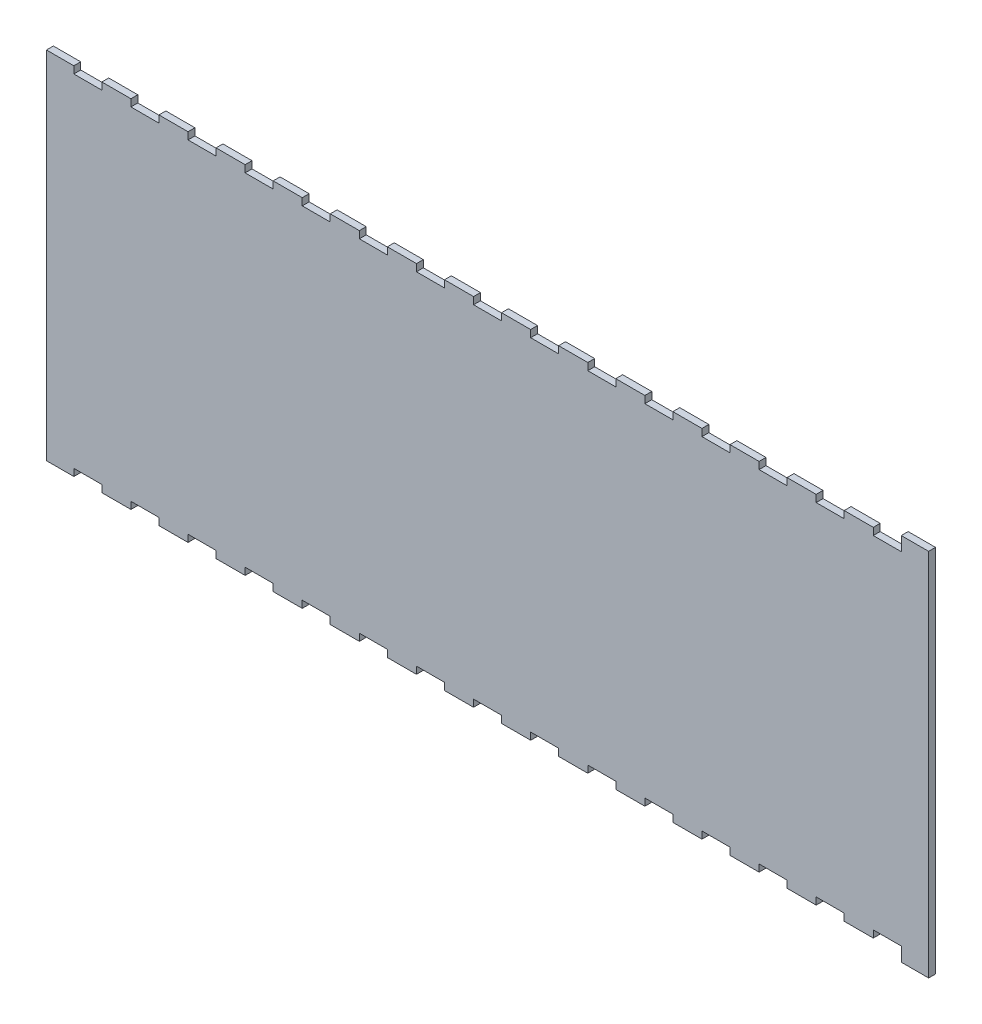
SolidWorks part; units mm, degrees
ref_plane "Front Plane" through (0, 0, 0) normal (0, 0, 1) x (1, 0, 0)
ref_plane "Top Plane" through (0, 0, 0) normal (0, 1, 0) x (1, 0, 0)
ref_plane "Right Plane" through (0, 0, 0) normal (1, 0, 0) x (0, 0, -1)
sketch "Sketch1" plane through (0, 0, 0) normal (0, 0, 1) x (1, 0, 0)
  line L248 (-12.6, 160.6058) -> (-25.5, 160.6058)
  line L249 (-25.5, 160.6058) -> (-25.5, 163.8808)
  line L250 (-25.5, 163.8808) -> (-38.9071, 163.8808)
  line L251 (-38.9071, 163.8808) -> (-38.9071, 160.6058)
  line L252 (-38.9071, 160.6058) -> (-51.8071, 160.6058)
  line L253 (-51.8071, 160.6058) -> (-51.8071, 163.8808)
  line L254 (-51.8071, 163.8808) -> (-65.2143, 163.8808)
  line L255 (-65.2143, 163.8808) -> (-65.2143, 160.6058)
  line L256 (-65.2143, 160.6058) -> (-78.1143, 160.6058)
  line L257 (-78.1143, 160.6058) -> (-78.1143, 163.8808)
  line L258 (-78.1143, 163.8808) -> (-91.5214, 163.8808)
  line L259 (-91.5214, 163.8808) -> (-91.5214, 160.6058)
  line L260 (-91.5214, 160.6058) -> (-104.4214, 160.6058)
  line L261 (-104.4214, 160.6058) -> (-104.4214, 163.8808)
  line L262 (-104.4214, 163.8808) -> (-117.8286, 163.8808)
  line L263 (-117.8286, 163.8808) -> (-117.8286, 160.6058)
  line L264 (-117.8286, 160.6058) -> (-130.7286, 160.6058)
  line L265 (-130.7286, 160.6058) -> (-130.7286, 163.8808)
  line L266 (-130.7286, 163.8808) -> (-144.1357, 163.8808)
  line L267 (-144.1357, 163.8808) -> (-144.1357, 160.6058)
  line L268 (-144.1357, 160.6058) -> (-157.0357, 160.6058)
  line L269 (-157.0357, 160.6058) -> (-157.0357, 163.8808)
  line L270 (-157.0357, 163.8808) -> (-170.4429, 163.8808)
  line L271 (-170.4429, 163.8808) -> (-170.4429, 160.6058)
  line L272 (-170.4429, 160.6058) -> (-183.3429, 160.6058)
  line L273 (-183.3429, 160.6058) -> (-183.3429, 163.8808)
  line L274 (-183.3429, 163.8808) -> (-196.75, 163.8808)
  line L275 (-196.75, 163.8808) -> (-196.75, 160.6058)
  line L276 (-196.75, 160.6058) -> (-209.65, 160.6058)
  line L277 (-209.65, 160.6058) -> (-209.65, 163.8808)
  line L278 (-209.65, 163.8808) -> (-223.0571, 163.8808)
  line L279 (-223.0571, 163.8808) -> (-223.0571, 160.6058)
  line L280 (-223.0571, 160.6058) -> (-235.9571, 160.6058)
  line L281 (-235.9571, 160.6058) -> (-235.9571, 163.8808)
  line L282 (-235.9571, 163.8808) -> (-249.3643, 163.8808)
  line L283 (-249.3643, 163.8808) -> (-249.3643, 160.6058)
  line L284 (-249.3643, 160.6058) -> (-262.2643, 160.6058)
  line L285 (-262.2643, 160.6058) -> (-262.2643, 163.8808)
  line L286 (-262.2643, 163.8808) -> (-275.6714, 163.8808)
  line L287 (-275.6714, 163.8808) -> (-275.6714, 160.6058)
  line L288 (-275.6714, 160.6058) -> (-288.5714, 160.6058)
  line L289 (-288.5714, 160.6058) -> (-288.5714, 163.8808)
  line L290 (-288.5714, 163.8808) -> (-301.9786, 163.8808)
  line L291 (-301.9786, 163.8808) -> (-301.9786, 160.6058)
  line L292 (-301.9786, 160.6058) -> (-314.8786, 160.6058)
  line L293 (-314.8786, 160.6058) -> (-314.8786, 163.8808)
  line L294 (-314.8786, 163.8808) -> (-328.2857, 163.8808)
  line L295 (-328.2857, 163.8808) -> (-328.2857, 160.6058)
  line L296 (-328.2857, 160.6058) -> (-341.1857, 160.6058)
  line L297 (-341.1857, 160.6058) -> (-341.1857, 163.8808)
  line L298 (-341.1857, 163.8808) -> (-354.5929, 163.8808)
  line L299 (-354.5929, 163.8808) -> (-354.5929, 160.6058)
  line L300 (-354.5929, 160.6058) -> (-367.4929, 160.6058)
  line L301 (-367.4929, 160.6058) -> (-367.4929, 163.8808)
  line L302 (-367.4929, 163.8808) -> (-380.9, 163.8808)
  line L303 (-380.9, 163.8808) -> (-380.9, 160.6058)
  line L304 (-380.9, 160.6058) -> (-393.8, 160.6058)
  line L305 (-393.8, 160.6058) -> (-393.8, 163.8808)
  line L306 (-393.8, 163.8808) -> (-406.4, 163.8808)
  line L307 (-406.4, 163.8808) -> (-406.4, 0)
  line L308 (-406.4, 0) -> (-393.8, 0)
  line L309 (-393.8, 0) -> (-393.8, 3.275)
  line L310 (-393.8, 3.275) -> (-380.9, 3.275)
  line L311 (-380.9, 3.275) -> (-380.9, 0)
  line L312 (-380.9, 0) -> (-367.4929, 0)
  line L313 (-367.4929, 0) -> (-367.4929, 3.275)
  line L314 (-367.4929, 3.275) -> (-354.5929, 3.275)
  line L315 (-354.5929, 3.275) -> (-354.5929, 0)
  line L316 (-354.5929, 0) -> (-341.1857, 0)
  line L317 (-341.1857, 0) -> (-341.1857, 3.275)
  line L318 (-341.1857, 3.275) -> (-328.2857, 3.275)
  line L319 (-328.2857, 3.275) -> (-328.2857, 0)
  line L320 (-328.2857, 0) -> (-314.8786, 0)
  line L321 (-314.8786, 0) -> (-314.8786, 3.275)
  line L322 (-314.8786, 3.275) -> (-301.9786, 3.275)
  line L323 (-301.9786, 3.275) -> (-301.9786, 0)
  line L324 (-301.9786, 0) -> (-288.5714, 0)
  line L325 (-288.5714, 0) -> (-288.5714, 3.275)
  line L326 (-288.5714, 3.275) -> (-275.6714, 3.275)
  line L327 (-275.6714, 3.275) -> (-275.6714, 0)
  line L328 (-275.6714, 0) -> (-262.2643, 0)
  line L329 (-262.2643, 0) -> (-262.2643, 3.275)
  line L330 (-262.2643, 3.275) -> (-249.3643, 3.275)
  line L331 (-249.3643, 3.275) -> (-249.3643, 0)
  line L332 (-249.3643, 0) -> (-235.9571, 0)
  line L333 (-235.9571, 0) -> (-235.9571, 3.275)
  line L334 (-235.9571, 3.275) -> (-223.0571, 3.275)
  line L335 (-223.0571, 3.275) -> (-223.0571, 0)
  line L336 (-223.0571, 0) -> (-209.65, 0)
  line L337 (-209.65, 0) -> (-209.65, 3.275)
  line L338 (-209.65, 3.275) -> (-196.75, 3.275)
  line L339 (-196.75, 3.275) -> (-196.75, 0)
  line L340 (-196.75, 0) -> (-183.3429, 0)
  line L341 (-183.3429, 0) -> (-183.3429, 3.275)
  line L342 (-183.3429, 3.275) -> (-170.4429, 3.275)
  line L343 (-170.4429, 3.275) -> (-170.4429, 0)
  line L344 (-170.4429, 0) -> (-157.0357, 0)
  line L345 (-157.0357, 0) -> (-157.0357, 3.275)
  line L346 (-157.0357, 3.275) -> (-144.1357, 3.275)
  line L347 (-144.1357, 3.275) -> (-144.1357, 0)
  line L348 (-144.1357, 0) -> (-130.7286, 0)
  line L349 (-130.7286, 0) -> (-130.7286, 3.275)
  line L350 (-130.7286, 3.275) -> (-117.8286, 3.275)
  line L351 (-117.8286, 3.275) -> (-117.8286, 0)
  line L352 (-117.8286, 0) -> (-104.4214, 0)
  line L353 (-104.4214, 0) -> (-104.4214, 3.275)
  line L354 (-104.4214, 3.275) -> (-91.5214, 3.275)
  line L355 (-91.5214, 3.275) -> (-91.5214, 0)
  line L356 (-91.5214, 0) -> (-78.1143, 0)
  line L357 (-78.1143, 0) -> (-78.1143, 3.275)
  line L358 (-78.1143, 3.275) -> (-65.2143, 3.275)
  line L359 (-65.2143, 3.275) -> (-65.2143, 0)
  line L360 (-65.2143, 0) -> (-51.8071, 0)
  line L361 (-51.8071, 0) -> (-51.8071, 3.275)
  line L362 (-51.8071, 3.275) -> (-38.9071, 3.275)
  line L363 (-38.9071, 3.275) -> (-38.9071, 0)
  line L364 (-38.9071, 0) -> (-25.5, 0)
  line L365 (-25.5, 0) -> (-25.5, 3.275)
  line L366 (-25.5, 3.275) -> (-12.6, 3.275)
  line L367 (-12.6, 3.275) -> (-12.6, -3.175)
  line L368 (-12.6, -3.175) -> (0, -3.175)
  line L369 (0, -3.175) -> (0, 167.0558)
  line L370 (0, 167.0558) -> (-12.6, 167.0558)
  line L371 (-12.6, 167.0558) -> (-12.6, 160.6058)
extrude "Boss-Extrude1" add sketch "Sketch1" along normal blind 3.175
